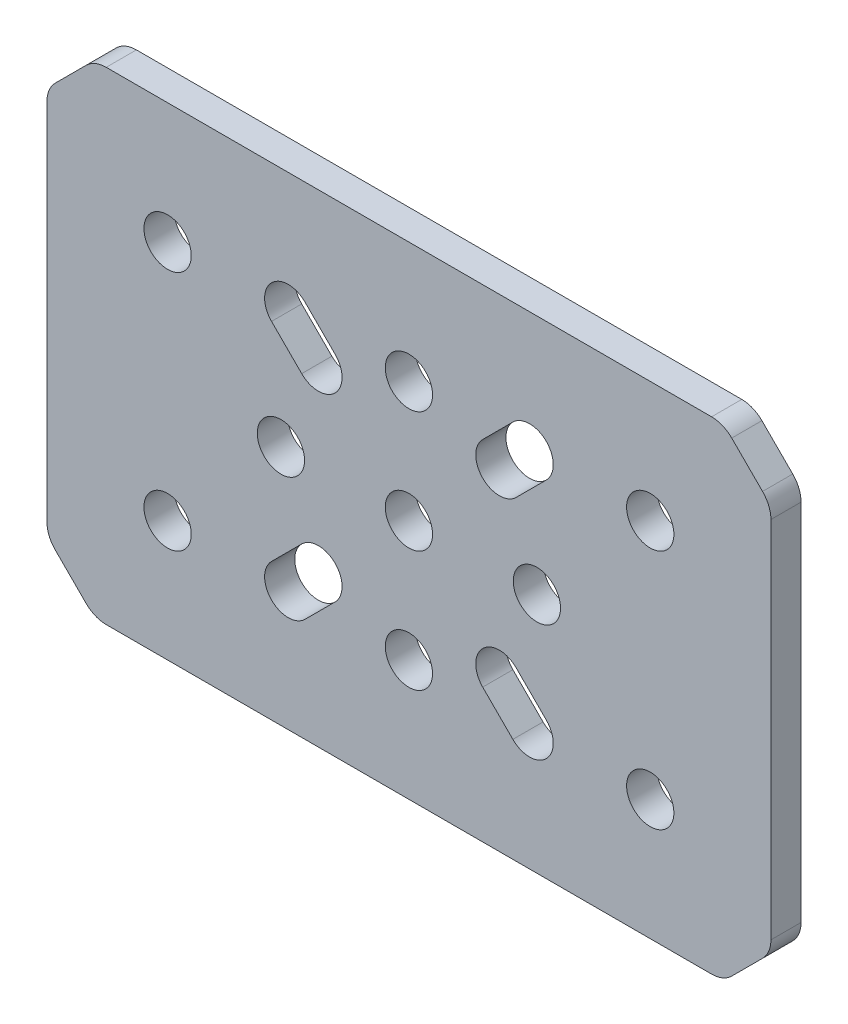
SolidWorks part; units mm, degrees
material "5052-H32"
ref_plane "Front Plane" through (0, 0, 0) normal (0, 0, 1) x (1, 0, 0)
ref_plane "Top Plane" through (0, 0, 0) normal (0, 1, 0) x (1, 0, 0)
ref_plane "Right Plane" through (0, 0, 0) normal (1, 0, 0) x (0, 0, -1)
sketch "Sketch1" plane through (0, 0, 0) normal (0, 0, 1) x (1, 0, 0)
  line L0 (11.2851, -7.7649) -> (14.4601, -10.9399)
  line L1 (10.9399, -14.4601) -> (7.7649, -11.2851)
  line L2 (-10.9399, 14.4601) -> (-7.7649, 11.2851)
  line L3 (-11.2851, 7.7649) -> (-14.4601, 10.9399)
  line L4 (-7.7649, -11.2851) -> (-10.9399, -14.4601)
  line L5 (-14.4601, -10.9399) -> (-11.2851, -7.7649)
  line L6 (14.4601, 10.9399) -> (11.2851, 7.7649)
  line L7 (7.7649, 11.2851) -> (10.9399, 14.4601)
  line L8 (33.9787, -24.5213) -> (37.2213, -21.2787)
  line L9 (38.1, -19.1574) -> (38.1, 19.1574)
  line L10 (37.2213, 21.2787) -> (33.9787, 24.5213)
  line L11 (31.8574, 25.4) -> (-31.8574, 25.4)
  line L12 (-33.9787, 24.5213) -> (-37.2213, 21.2787)
  line L13 (-38.1, 19.1574) -> (-38.1, -19.1574)
  line L14 (-37.2213, -21.2787) -> (-33.9787, -24.5213)
  line L15 (-31.8574, -25.4) -> (31.8574, -25.4)
  line L16 (-12.7, 12.7) -> (12.7, -12.7) construction
  line L17 (-12.7, -12.7) -> (12.7, 12.7) construction
  circle A0 centre (13.4704, 0) radius 2.4892
  arc A1 (7.7649, -11.2851) -> (11.2851, -7.7649) centre (9.525, -9.525) cw
  arc A2 (14.4601, -10.9399) -> (10.9399, -14.4601) centre (12.7, -12.7) cw
  arc A3 (-14.4601, 10.9399) -> (-10.9399, 14.4601) centre (-12.7, 12.7) cw
  arc A4 (-7.7649, 11.2851) -> (-11.2851, 7.7649) centre (-9.525, 9.525) cw
  circle A5 centre (-25.4, 12.7) radius 2.4892
  circle A6 centre (25.4, 12.7) radius 2.4892
  circle A7 centre (25.4, -12.7) radius 2.4892
  circle A8 centre (0, -12.7) radius 2.4892
  arc A9 (-11.2851, -7.7649) -> (-7.7649, -11.2851) centre (-9.525, -9.525) cw
  arc A10 (-10.9399, -14.4601) -> (-14.4601, -10.9399) centre (-12.7, -12.7) cw
  circle A11 centre (-25.4, -12.7) radius 2.4892
  circle A12 centre (0, 12.7) radius 2.4892
  circle A13 centre (0, 0) radius 2.4892
  arc A14 (10.9399, 14.4601) -> (14.4601, 10.9399) centre (12.7, 12.7) cw
  arc A15 (11.2851, 7.7649) -> (7.7649, 11.2851) centre (9.525, 9.525) cw
  circle A16 centre (-13.4704, 0) radius 2.4892
  arc A17 (37.2213, -21.2787) -> (38.1, -19.1574) centre (35.1, -19.1574) ccw
  arc A18 (38.1, 19.1574) -> (37.2213, 21.2787) centre (35.1, 19.1574) ccw
  arc A19 (33.9787, 24.5213) -> (31.8574, 25.4) centre (31.8574, 22.4) ccw
  arc A20 (-31.8574, 25.4) -> (-33.9787, 24.5213) centre (-31.8574, 22.4) ccw
  arc A21 (-37.2213, 21.2787) -> (-38.1, 19.1574) centre (-35.1, 19.1574) ccw
  arc A22 (-38.1, -19.1574) -> (-37.2213, -21.2787) centre (-35.1, -19.1574) ccw
  arc A23 (-33.9787, -24.5213) -> (-31.8574, -25.4) centre (-31.8574, -22.4) ccw
  arc A24 (31.8574, -25.4) -> (33.9787, -24.5213) centre (31.8574, -22.4) ccw
  point P66 (0, 0)
  point P67 (0, 0)
  point P68 (0, 0)
  point P69 (0, 0)
  point P71 (0, 0)
  point P72 (0, 0)
  dimension "D1" = 3
  dimension "D2" = 4.9784
extrude "Boss-Extrude1" add sketch "Sketch1" against normal blind 3.175
